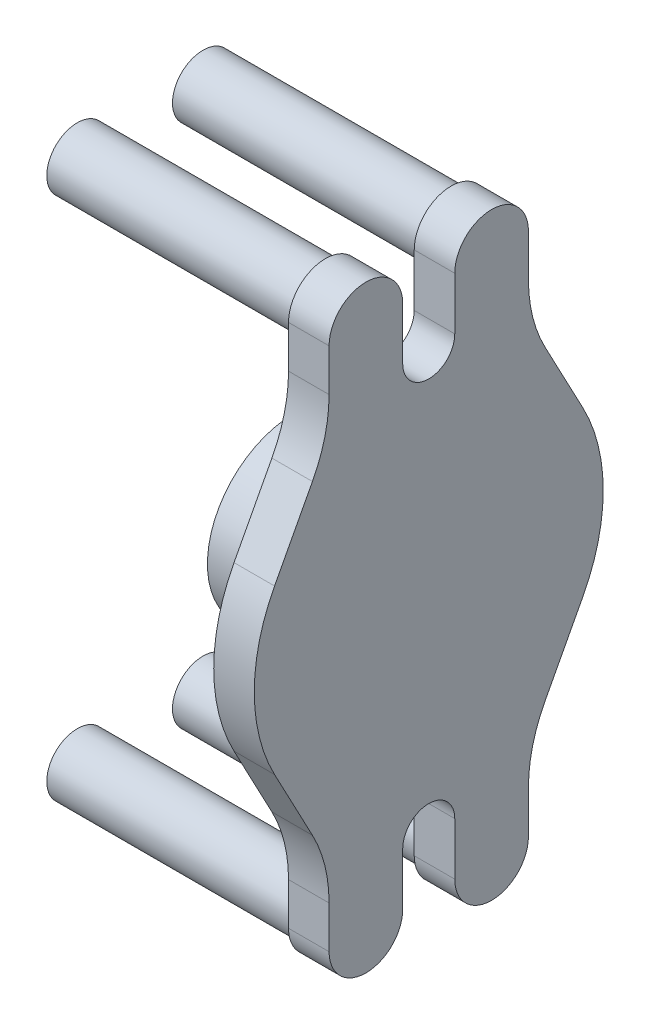
SolidWorks part; units mm, degrees
ref_plane "Front Plane" through (0, 0, 0) normal (0, 0, 1) x (1, 0, 0)
ref_plane "Top Plane" through (0, 0, 0) normal (0, 1, 0) x (1, 0, 0)
ref_plane "Right Plane" through (0, 0, 0) normal (1, 0, 0) x (0, 0, -1)
sketch "Sketch1" plane through (0, 0, 0) normal (0, 0, 1) x (1, 0, 0)
  line L0 (8.255, 0) -> (-8.255, 0) construction
  line L1 (27.9, 0) -> (-27.9, 0) construction
  line L2 (8.255, 0) -> (8.255, 18.25)
  line L3 (8.255, 18.25) -> (27.9, 18.25)
  line L4 (27.9, 18.25) -> (27.9, 0)
  line L5 (8.255, 0) -> (27.9, 0)
  point P4 (0, 0)
  point P8 (0, 0)
  dimension "D1" = 16.51
  dimension "D2" = 19.645
  dimension "D3" = 18.25
revolve "Revolve1" add sketch "Sketch1" angle 360 about L5
sketch "Sketch2" plane through (8.255, 0, 0) normal (-1, 0, 0) x (0, 0, 1)
  circle A0 centre (0, 0) radius 2.3935
  dimension "D1" = 4.787
extrude "Cut-Extrude1" cut sketch "Sketch2" against normal blind 8.5725
sketch "Sketch3" plane through (27.9, 0, 0) normal (1, 0, 0) x (0, 0, -1)
  line L0 (-20.8953, -55) -> (-20.8953, -46.1532)
  line L1 (13.175, -55) -> (-13.175, -55) construction
  line L2 (13.175, -55) -> (13.175, 55) construction
  line L3 (13.175, 55) -> (-13.175, 55) construction
  line L4 (-13.175, -55) -> (-13.175, 55) construction
  line L5 (13.175, -55) -> (-13.175, 55) construction
  line L6 (13.175, 55) -> (-13.175, -55) construction
  line L7 (-24.3823, -32.1152) -> (-32.3245, -17.1152)
  line L9 (-5.4548, -55) -> (-5.4548, -44)
  line L11 (5.4547, -44) -> (5.4547, -55)
  line L12 (20.8953, -55) -> (20.8953, -46.1532)
  line L13 (24.3823, -32.1152) -> (32.3245, -17.1152)
  line L14 (55, 0) -> (-55, 0) construction
  line L15 (13.175, -55) -> (-13.175, 55) construction
  line L16 (13.175, 55) -> (-13.175, -55) construction
  line L17 (13.175, 55) -> (-13.175, 55) construction
  line L18 (24.3823, 32.1152) -> (32.3245, 17.1152)
  line L19 (20.8953, 55) -> (20.8953, 46.1532)
  line L20 (5.4547, 44) -> (5.4547, 55)
  line L21 (-5.4548, 55) -> (-5.4548, 44)
  line L22 (-24.3823, 32.1152) -> (-32.3245, 17.1152)
  line L23 (-20.8953, 55) -> (-20.8953, 46.1532)
  arc A15 (32.3245, -17.1152) -> (32.3245, 17.1152) centre (0, 0) ccw
  arc A16 (-5.4548, 55) -> (-20.8953, 55) centre (-13.175, 55) ccw
  arc A17 (-20.8953, -55) -> (-5.4548, -55) centre (-13.175, -55) ccw
  arc A18 (5.4547, -55) -> (20.8953, -55) centre (13.175, -55) ccw
  arc A19 (20.8953, 55) -> (5.4547, 55) centre (13.175, 55) ccw
  arc A20 (-5.4548, -44) -> (5.4547, -44) centre (0, -44) cw
  arc A21 (20.8953, -46.1532) -> (24.3823, -32.1152) centre (50.8953, -46.1532) cw
  arc A22 (-20.8953, -46.1532) -> (-24.3823, -32.1152) centre (-50.8953, -46.1532) ccw
  arc A23 (-20.8953, 46.1532) -> (-24.3823, 32.1152) centre (-50.8953, 46.1532) cw
  arc A24 (20.8953, 46.1532) -> (24.3823, 32.1152) centre (50.8953, 46.1532) ccw
  arc A25 (-5.4548, 44) -> (5.4547, 44) centre (0, 44) ccw
  arc A26 (5.4547, 55) -> (20.8953, 55) centre (13.175, 55) cw
  arc A27 (-20.8953, 55) -> (-5.4548, 55) centre (-13.175, 55) cw
  arc A29 (-32.3245, 17.1152) -> (-32.3245, -17.1152) centre (0, 0) ccw
  circle M2 centre (0, 0) radius 18.25
  dimension "D3" = 15.4405
  dimension "D5" = 7.7203
  dimension "D4" = 30
  dimension "D7" = 15
  dimension "D9" = 110
  dimension "D1" = 73.152
  dimension "D6" = 15
  dimension "D2" = 26.35
  dimension "D8" = 11
extrude "Boss-Extrude1" add sketch "Sketch3" along normal blind 8.5 separate body contours L22 A29 L7 A22 L0 A17 L9 A20 L11 A18 L12 A21 L13 A15 L18 A24 L19 A19 L20 A25 L21 A16 L23 A23 M2 | M2
sketch "Sketch4" plane through (27.9, 0, 0) normal (-1, 0, 0) x (0, 0, 1)
  line L0 (-20.8953, 55) -> (-5.4547, 55) construction
  line L1 (13.175, -55) -> (-13.175, -55) construction
  line L2 (13.175, -55) -> (13.175, 55) construction
  line L3 (13.175, 55) -> (-13.175, 55) construction
  line L4 (-13.175, -55) -> (-13.175, 55) construction
  line L5 (13.175, -55) -> (-13.175, 55) construction
  line L6 (13.175, 55) -> (-13.175, -55) construction
  circle A0 centre (-13.175, 55) radius 4.75
  circle A1 centre (13.175, -55) radius 4.75
  circle A2 centre (13.175, 55) radius 4.75
  circle A3 centre (-13.175, -55) radius 4.75
  arc A4 (-5.4547, 55) -> (-20.8953, 55) centre (-13.175, 55) ccw construction
  circle A5 centre (-13.175, 55) radius 6.4
  circle A6 centre (13.175, 55) radius 6.4
  circle A7 centre (13.175, -55) radius 6.4
  circle A8 centre (-13.175, -55) radius 6.4
  point P6 (0, 0)
  dimension "D1" = 9.5
  dimension "D2" = 12.8
extrude "Boss-Extrude2" add sketch "Sketch4" along normal blind 52
sketch "Sketch5" plane through (8.255, 0, 0) normal (-1, 0, 0) x (0, 0, 1)
  circle A0 centre (0, 0) radius 18.25
  dimension "D1" = 36.5
